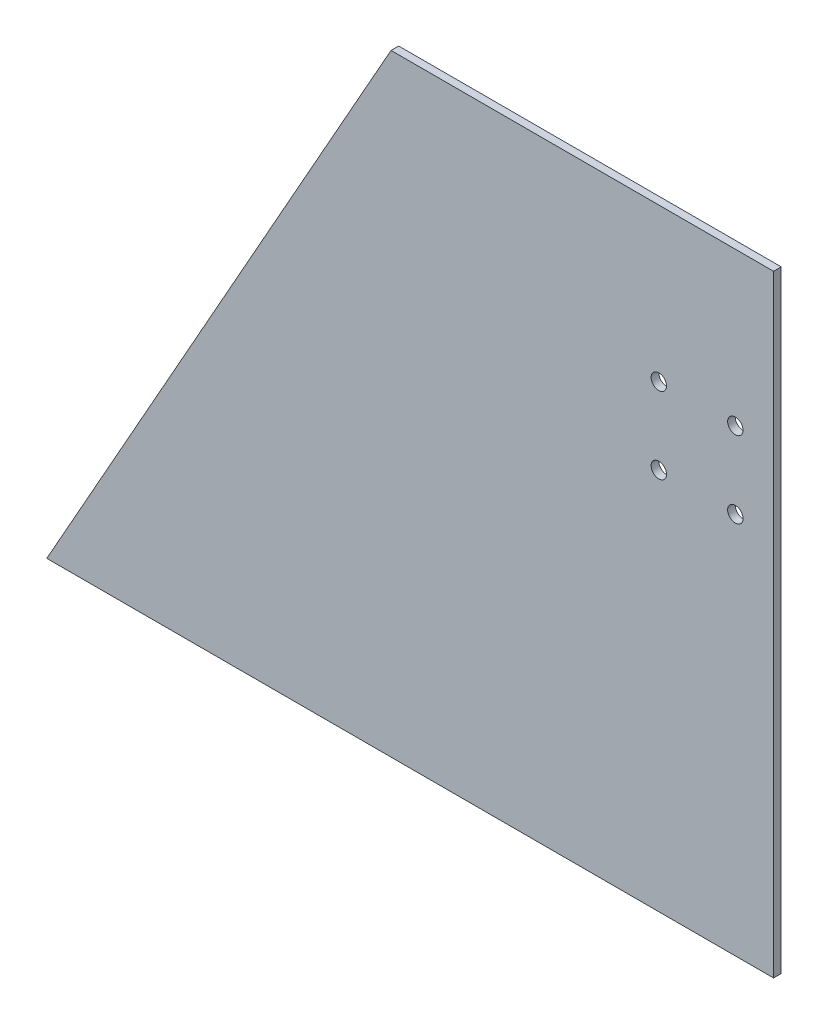
SolidWorks part; units mm, degrees
material "Acrylic (Medium-high impact)"
ref_plane "Front Plane" through (0, 0, 0) normal (0, 0, 1) x (1, 0, 0)
ref_plane "Top Plane" through (0, 0, 0) normal (0, 1, 0) x (1, 0, 0)
ref_plane "Right Plane" through (0, 0, 0) normal (1, 0, 0) x (0, 0, -1)
sketch "Sketch1" plane through (0, 0, 0) normal (0, 0, 1) x (1, 0, 0)
  line L0 (0, 0) -> (241.3, 0)
  line L1 (241.3, 0) -> (241.3, 203.2)
  line L2 (241.3, 203.2) -> (114.3, 203.2)
  line L3 (114.3, 203.2) -> (0, 0)
  dimension "D1" = 203.2
  dimension "D2" = 241.3
  dimension "D3" = 127
extrude "Boss-Extrude1" add sketch "Sketch1" along normal blind 2.54
hole_wizard "#10 Clearance Hole1" positions "Sketch3" profile "Sketch2" hole size "#10" standard "ANSI Inch" end condition through all
sketch "Sketch3" plane through (0, 0, 2.54) normal (0, 0, 1) x (1, 0, 0)
  line L1 (203.2, 152.4) -> (228.6, 152.4) construction
  line L2 (203.2, 152.4) -> (203.2, 127) construction
  line L3 (203.2, 127) -> (228.6, 127) construction
  line L4 (228.6, 152.4) -> (228.6, 127) construction
  line L5 (241.3, 203.2) -> (114.3, 203.2) construction
  line L6 (241.3, 0) -> (241.3, 203.2) construction
  point P1 (203.2, 152.4)
  point P2 (228.6, 127)
  point P35 (203.2, 127)
  point P36 (228.6, 152.4)
  dimension "D1" = 25.4
  dimension "D2" = 25.4
  dimension "D3" = 50.8
  dimension "D4" = 12.7
sketch "Sketch2" plane through (203.2, 152.4, 2.54) normal (1, 0, 0) x (0, -1, 0)
  line L0 (0, 0) -> (0, 2.54)
  line L1 (0, 2.54) -> (2.5527, 2.54)
  line L2 (2.5527, 2.54) -> (2.5527, 0)
  line L5 (2.5527, 0) -> (0, 0)
  line L11 (0, -6.35) -> (0, 107.95) construction
  dimension "Thru Hole Dia." = 5.1054
  dimension "Thru Hole Depth" = 2.54
